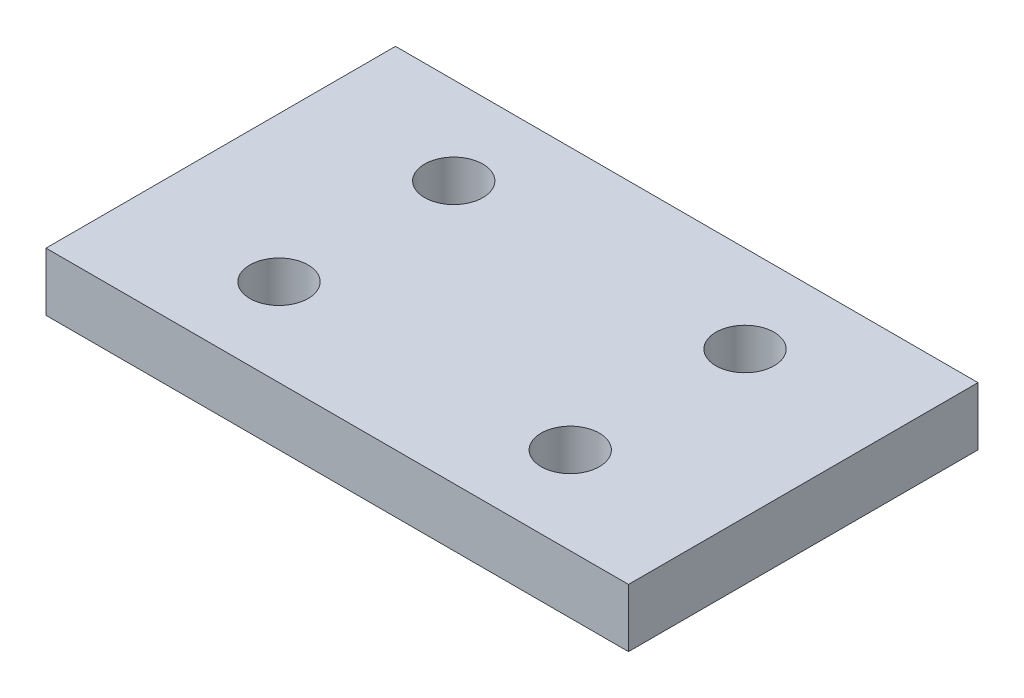
SolidWorks part; units mm, degrees
ref_plane "Спереди" through (0, 0, 0) normal (0, 0, 1) x (1, 0, 0)
ref_plane "Сверху" through (0, 0, 0) normal (0, 1, 0) x (1, 0, 0)
ref_plane "Справа" through (0, 0, 0) normal (1, 0, 0) x (0, 0, -1)
sketch "Эскиз1" plane through (0, 0, 0) normal (0, 1, 0) x (1, 0, 0)
  line L1 (0, 0) -> (100, 0)
  line L2 (0, 0) -> (0, 60)
  line L3 (0, 60) -> (100, 60)
  line L4 (100, 0) -> (100, 60)
extrude "Бобышка-Вытянуть1" add sketch "Эскиз1" along normal blind 10
sketch "Эскиз2" plane through (0, 10, 0) normal (0, 1, 0) x (1, 0, 0)
  circle A0 centre (25, 15) radius 5
  circle A1 centre (75, 15) radius 5
  circle A2 centre (25, 45) radius 5
  circle A3 centre (75, 45) radius 5
  dimension "D1" = 2
  dimension "D2" = 2
extrude "Вырез-Вытянуть1" cut sketch "Эскиз2" against normal through all
